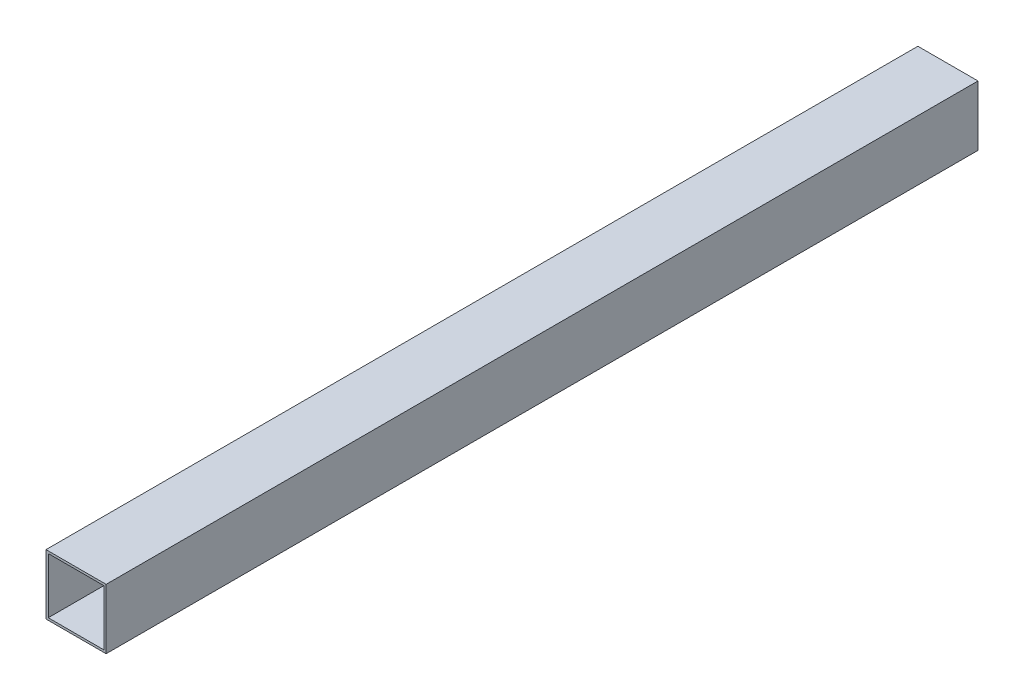
SolidWorks part; units mm, degrees
ref_plane "Plan de face" through (0, 0, 0) normal (0, 0, 1) x (1, 0, 0)
ref_plane "Plan de dessus" through (0, 0, 0) normal (0, 1, 0) x (1, 0, 0)
ref_plane "Plan de droite" through (0, 0, 0) normal (1, 0, 0) x (0, 0, -1)
sketch "Esquisse1" plane through (0, 0, 0) normal (0, 0, 1) x (1, 0, 0)
  line L1 (-20, -20) -> (20, -20)
  line L2 (-20, -20) -> (-20, 20)
  line L3 (-20, 20) -> (20, 20)
  line L4 (20, -20) -> (20, 20)
  line L5 (-20, -20) -> (20, 20) construction
  line L6 (-20, 20) -> (20, -20) construction
  line L7 (-18.5, -18.5) -> (18.5, -18.5)
  line L8 (-18.5, -18.5) -> (-18.5, 18.5)
  line L9 (-18.5, 18.5) -> (18.5, 18.5)
  line L10 (18.5, -18.5) -> (18.5, 18.5)
  line L11 (-18.5, -18.5) -> (18.5, 18.5) construction
  line L12 (-18.5, 18.5) -> (18.5, -18.5) construction
  point P0 (0, 0)
  point P6 (0, 0)
  dimension "D1" = 40
  dimension "D2" = 40
  dimension "D3" = 37
  dimension "D4" = 37
extrude "Boss.-Extru.1" add sketch "Esquisse1" along normal blind 580
